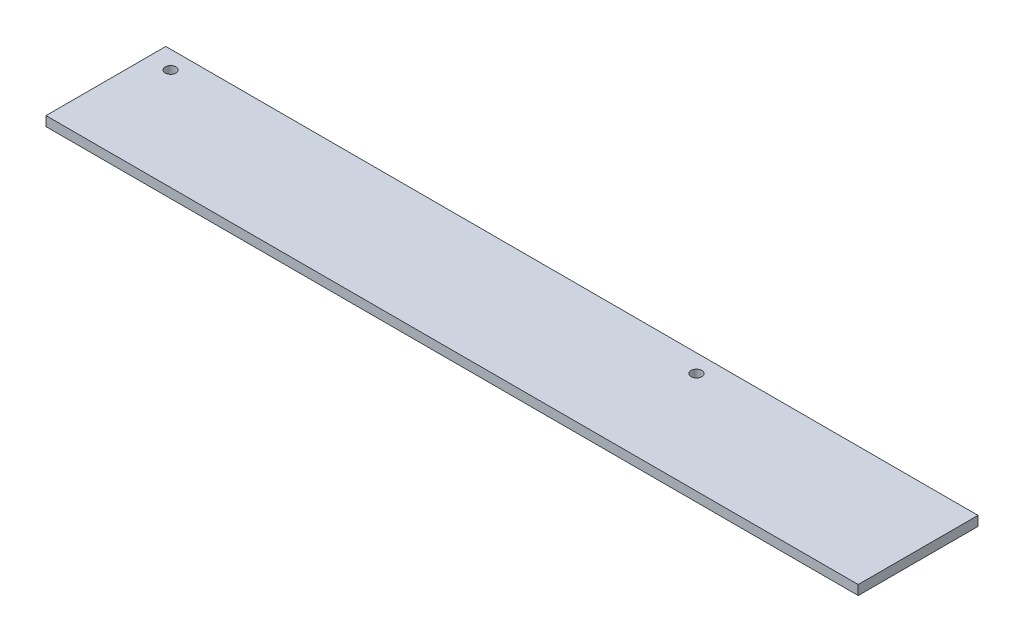
SolidWorks part; units mm, degrees
ref_plane "Спереди" through (0, 0, 0) normal (0, 0, 1) x (1, 0, 0)
ref_plane "Сверху" through (0, 0, 0) normal (0, 1, 0) x (1, 0, 0)
ref_plane "Справа" through (0, 0, 0) normal (1, 0, 0) x (0, 0, -1)
sketch "Эскиз1" plane through (0, 0, 0) normal (1, 0, 0) x (0, 0, -1)
  line L1 (-25, -2) -> (25, -2)
  line L2 (-25, -2) -> (-25, 2)
  line L3 (-25, 2) -> (25, 2)
  line L4 (25, -2) -> (25, 2)
  line L5 (-25, -2) -> (25, 2) construction
  line L6 (-25, 2) -> (25, -2) construction
  point P0 (0, 0)
  dimension "D1" = 4
  dimension "D2" = 50
extrude "Бобышка-Вытянуть1" add sketch "Эскиз1" along normal blind 339
sketch "Эскиз2" plane through (0, 2, 0) normal (0, 1, 0) x (1, 0, 0)
  line L0 (0, 25) -> (0, -25) construction
  line L1 (339, 25) -> (0, 25) construction
  line L2 (339, 25) -> (339, -25) construction
  circle A0 centre (9.5, 17.5) radius 2.25
  circle A1 centre (229, 17.5) radius 2.25
  dimension "D1" = 4.5
  dimension "D2" = 9.5
  dimension "D3" = 7.5
  dimension "D4" = 4.5
  dimension "D5" = 110
  dimension "D6" = 7.5
extrude "Вырез-Вытянуть1" cut sketch "Эскиз2" against normal through all
